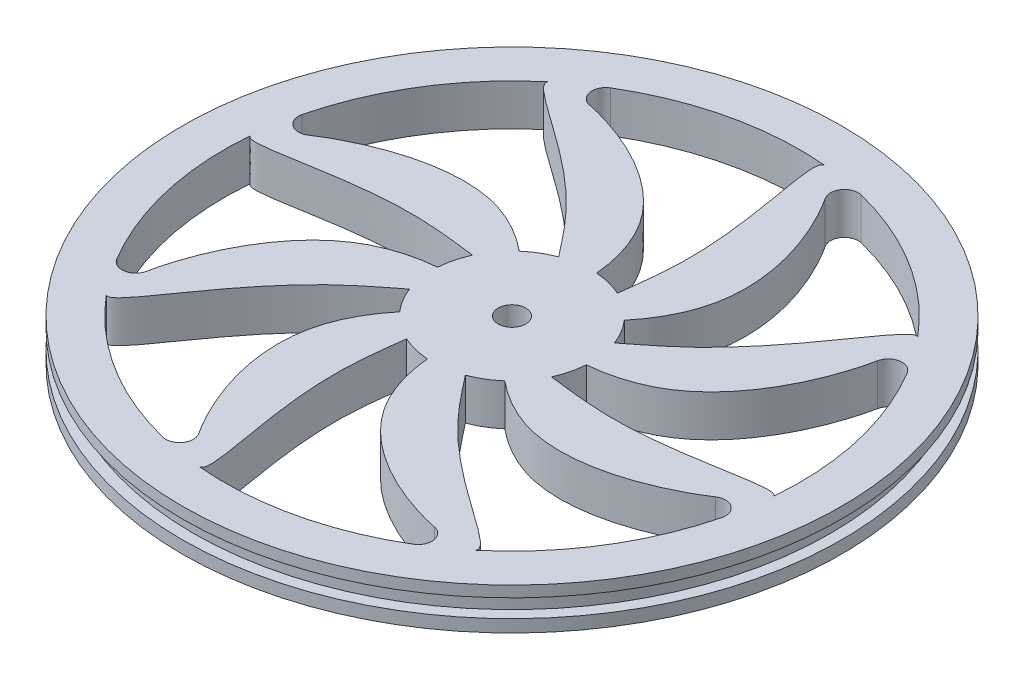
SolidWorks part; units mm, degrees
ref_plane "Front Plane" through (0, 0, 0) normal (0, 0, 1) x (1, 0, 0)
ref_plane "Top Plane" through (0, 0, 0) normal (0, 1, 0) x (1, 0, 0)
ref_plane "Right Plane" through (0, 0, 0) normal (1, 0, 0) x (0, 0, -1)
sketch "Sketch1" plane through (0, 0, 0) normal (0, 0, 1) x (1, 0, 0)
  line L0 (0, 57.5678) -> (0, -54.0899) construction
  line L1 (-62.7846, 0) -> (56.642, 0) construction
  line L3 (52.832, 3.81) -> (60.452, 3.81)
  line L4 (52.832, 3.81) -> (52.832, -3.81)
  line L5 (52.832, -3.81) -> (60.452, -3.81)
  line L6 (60.452, 3.81) -> (60.452, -3.81)
  line L7 (52.832, 3.81) -> (60.452, -3.81) construction
  line L8 (52.832, -3.81) -> (60.452, 3.81) construction
  line L13 (60.452, 1.778) -> (58.42, 1.778)
  line L14 (60.452, 1.778) -> (60.452, -1.524)
  line L15 (60.452, -1.524) -> (58.42, -1.524)
  line L16 (58.42, 1.778) -> (58.42, -1.524)
  dimension "D1" = 52.832
  dimension "D2" = 7.62
  dimension "D3" = 7.62
  dimension "D4" = 2.032
  dimension "D5" = 3.302
  dimension "D6" = 2.286
revolve "Revolve1" add sketch "Sketch1" angle 360 about L0
sketch "Sketch2" plane through (0, 0, 0) normal (0, 1, 0) x (1, 0, 0)
  circle A1 centre (0, 0) radius 2.54
  circle A2 centre (0, 0) radius 52.832 construction
  circle A3 centre (0, 0) radius 14.605
  spline S0 degree 3 poles (-13.338, 28.1657) (2.0331, 1.6305) (0.5791, 37.1758) (-51.8798, 46.4086) (-13.338, 28.1657) (2.0331, 1.6305) (0.5791, 37.1758) knots -0.842686 -0.474329 -0.168006 0 0.157314 0.525671 0.831994 1 1.157314 1.525671 1.831994 only from (0, 9.2722) to (0, 9.2722)
  spline S1 degree 3 poles (10.4848, 29.3476) (2.5906, -0.2846) (26.6968, 25.8778) (-3.8687, 69.5004) (10.4848, 29.3476) (2.5906, -0.2846) (26.6968, 25.8778) knots -0.842686 -0.474329 -0.168006 0 0.157314 0.525671 0.831994 1 1.157314 1.525671 1.831994 only from (6.5565, 6.5565) to (6.5565, 6.5565)
  spline S2 degree 3 poles (28.1657, 13.338) (1.6305, -2.0331) (37.1758, -0.5791) (46.4086, 51.8798) (28.1657, 13.338) (1.6305, -2.0331) (37.1758, -0.5791) knots -0.842686 -0.474329 -0.168006 0 0.157314 0.525671 0.831994 1 1.157314 1.525671 1.831994 only from (9.2722, 0) to (9.2722, 0)
  spline S3 degree 3 poles (29.3476, -10.4848) (-0.2846, -2.5906) (25.8778, -26.6968) (69.5004, 3.8687) (29.3476, -10.4848) (-0.2846, -2.5906) (25.8778, -26.6968) knots -0.842686 -0.474329 -0.168006 0 0.157314 0.525671 0.831994 1 1.157314 1.525671 1.831994 only from (6.5565, -6.5565) to (6.5565, -6.5565)
  spline S4 degree 3 poles (13.338, -28.1657) (-2.0331, -1.6305) (-0.5791, -37.1758) (51.8798, -46.4086) (13.338, -28.1657) (-2.0331, -1.6305) (-0.5791, -37.1758) knots -0.842686 -0.474329 -0.168006 0 0.157314 0.525671 0.831994 1 1.157314 1.525671 1.831994 only from (0, -9.2722) to (0, -9.2722)
  spline S5 degree 3 poles (-10.4848, -29.3476) (-2.5906, 0.2846) (-26.6968, -25.8778) (3.8687, -69.5004) (-10.4848, -29.3476) (-2.5906, 0.2846) (-26.6968, -25.8778) knots -0.842686 -0.474329 -0.168006 0 0.157314 0.525671 0.831994 1 1.157314 1.525671 1.831994 only from (-6.5565, -6.5565) to (-6.5565, -6.5565)
  spline S6 degree 3 poles (-28.1657, -13.338) (-1.6305, 2.0331) (-37.1758, 0.5791) (-46.4086, -51.8798) (-28.1657, -13.338) (-1.6305, 2.0331) (-37.1758, 0.5791) knots -0.842686 -0.474329 -0.168006 0 0.157314 0.525671 0.831994 1 1.157314 1.525671 1.831994 only from (-9.2722, 0) to (-9.2722, 0)
  spline S7 degree 3 poles (-29.3476, 10.4848) (0.2846, 2.5906) (-25.8778, 26.6968) (-69.5004, -3.8687) (-29.3476, 10.4848) (0.2846, 2.5906) (-25.8778, 26.6968) knots -0.842686 -0.474329 -0.168006 0 0.157314 0.525671 0.831994 1 1.157314 1.525671 1.831994 only from (-6.5565, 6.5565) to (-6.5565, 6.5565)
  point P41 (0, 0)
  dimension "D1" = 29.21
  dimension "D2" = 5.08
extrude "Boss-Extrude1" add sketch "Sketch2" along normal mid plane 7.62 contours A3 S5 | A3 S6 | A3 S7 | A3 S0 | A3 S1 | A3 S2 | A3 S3 | A3 S4 | S7 A3 S6 S5 S4 S3 S2 S1 S0 A1 | A3 S4 | A3 S5 | A3 S6 | A3 S7 | A3 S3 | A3 S2 | A3 S1 | A3 S0
fillet "Fillet1" radius 2.54 1 edges at (-5.2333, 0, 52.5722)
fillet "Fillet2" radius 2.54 7 edges at (33.4736, 0, 40.8747) (52.5722, 0, 5.2333) (40.8747, 0, -33.4736) (5.2333, 0, -52.5722) (-33.4736, 0, -40.8747) (-52.5722, 0, -5.2333) (-40.8747, 0, 33.4736)
